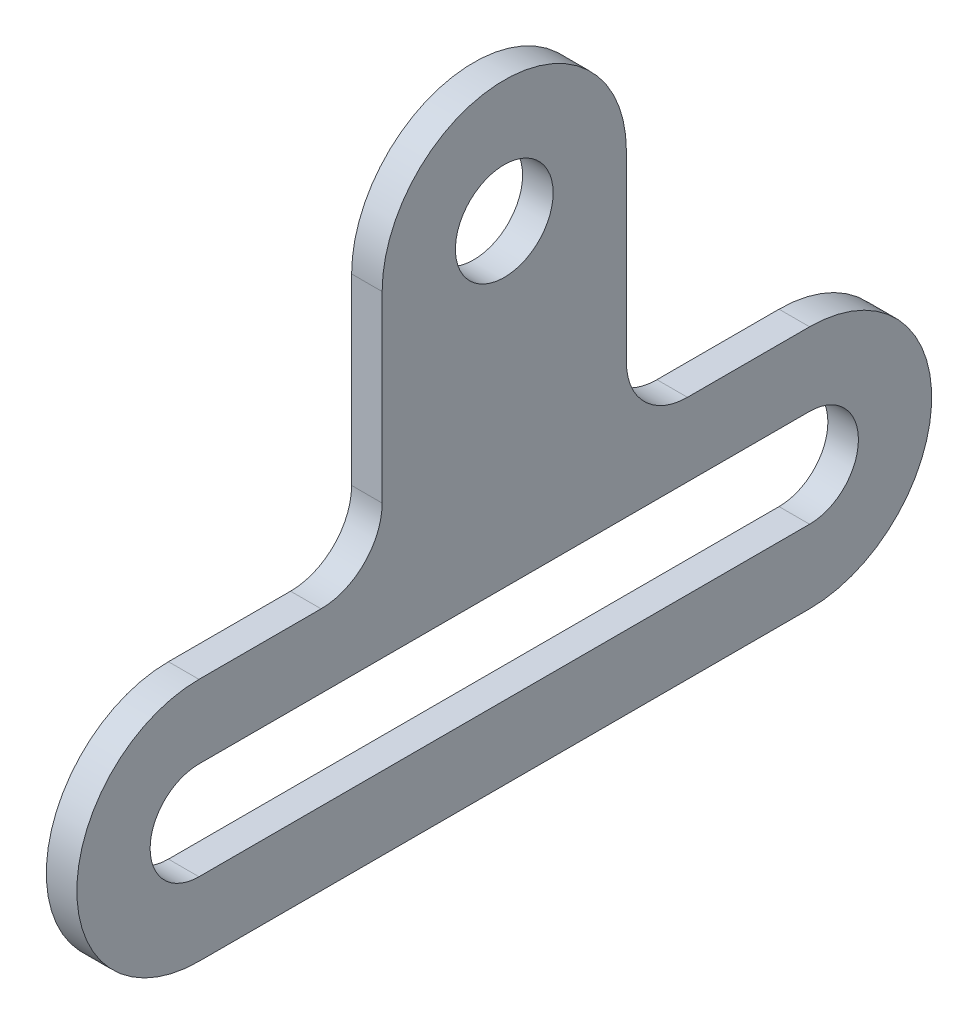
SolidWorks part; units mm, degrees
ref_plane "Front Plane" through (0, 0, 0) normal (0, 0, 1) x (1, 0, 0)
ref_plane "Top Plane" through (0, 0, 0) normal (0, 1, 0) x (1, 0, 0)
ref_plane "Right Plane" through (0, 0, 0) normal (1, 0, 0) x (0, 0, -1)
sketch "Sketch1" plane through (0, 0, 0) normal (1, 0, 0) x (0, 0, -1)
  line L0 (-10, 0) -> (10, 0) construction
  line L1 (-10, 4) -> (-6, 4)
  line L2 (-10, -4) -> (10, -4)
  line L3 (0, 12) -> (0, -6.3558) construction
  line L4 (-4, 6) -> (-4, 12)
  line L5 (4, 6) -> (4, 12)
  line L6 (6, 4) -> (10, 4)
  line L7 (-10, 1.6) -> (10, 1.6)
  line L8 (-10, -1.6) -> (10, -1.6)
  arc A0 (-10, 4) -> (-10, -4) centre (-10, 0) ccw
  arc A1 (10, -4) -> (10, 4) centre (10, 0) ccw
  arc A2 (10, -1.6) -> (10, 1.6) centre (10, 0) ccw
  arc A3 (-10, 1.6) -> (-10, -1.6) centre (-10, 0) ccw
  arc A5 (4, 12) -> (-4, 12) centre (0, 12) ccw
  circle A6 centre (0, 12) radius 1.6
  arc A7 (4, 6) -> (6, 4) centre (6, 6) ccw
  arc A8 (-4, 6) -> (-6, 4) centre (-6, 6) cw
  point P3 (0, 0)
  point P21 (4, 4)
  point P24 (-4, 4)
  dimension "D3" = 4
  dimension "D4" = 3.2
  dimension "D5" = 8
  dimension "D9" = 10
  dimension "D10" = 4
  dimension "D11" = 2
  dimension "D1" = 8
  dimension "D2" = 20
  dimension "D6" = 4
  dimension "D7" = 4
  dimension "D8" = 8
extrude "Boss-Extrude1" add sketch "Sketch1" along normal mid plane 1
